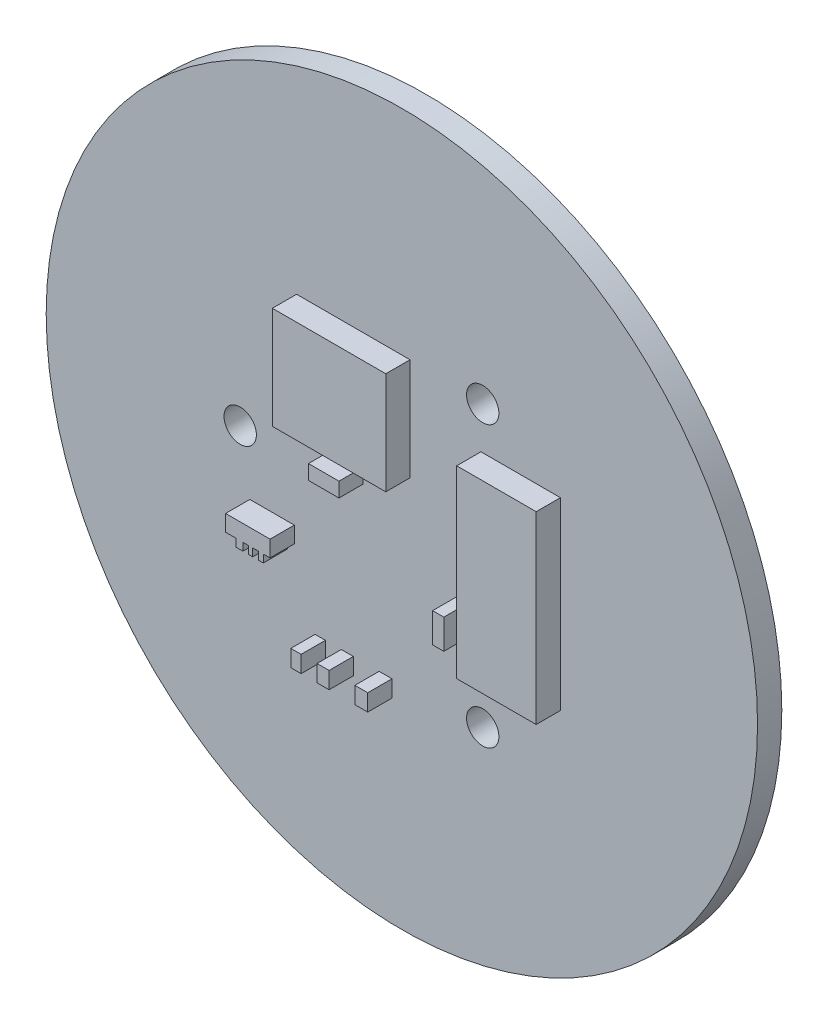
SolidWorks part; units mm, degrees
ref_plane "前视基准面" through (0, 0, 0) normal (0, 0, 1) x (1, 0, 0)
ref_plane "上视基准面" through (0, 0, 0) normal (0, 1, 0) x (1, 0, 0)
ref_plane "右视基准面" through (0, 0, 0) normal (1, 0, 0) x (0, 0, -1)
sketch "草图1" plane through (0, 0, 0) normal (0, 0, 1) x (1, 0, 0)
  circle A0 centre (0, 0) radius 22
extrude "凸台-拉伸1" add sketch "草图1" along normal blind 1.5
sketch "草图2" plane through (0, 0, 0) normal (0, 0, -1) x (-1, 0, 0)
  line L2 (2, 2.5) -> (2, -2.5)
  line L7 (-2, -2.5) -> (-2, 2.5)
  line L8 (2, -2.5) -> (-2, -2.5)
  line L9 (-2, 2.5) -> (2, 2.5)
extrude "凸台-拉伸2" add sketch "草图2" along normal blind 1.8
sketch "草图3" plane through (0, 0, 0) normal (0, 0, -1) x (-1, 0, 0)
  circle A1 centre (10, 0) radius 1
  circle A2 centre (-5, 8.6603) radius 1
  circle A3 centre (-5, -8.6603) radius 1
extrude "切除-拉伸1" cut sketch "草图3" against normal blind 1.8
sketch "草图4" plane through (0, 0, 1.5) normal (0, 0, 1) x (1, 0, 0)
  line L0 (-8.1056, -3.6542) -> (-6.6543, -3.6542)
  line L1 (-6.511, 8.7833) -> (0.5049, 8.7833)
  line L2 (-6.511, 8.7833) -> (-6.511, 2.4582)
  line L3 (-6.511, 2.4582) -> (0.5049, 2.4582)
  line L4 (0.5049, 8.7833) -> (0.5049, 2.4582)
  line L5 (4.8899, 6.046) -> (9.8064, 6.046)
  line L6 (4.8899, 6.046) -> (4.8899, -5.355)
  line L7 (4.8899, -5.355) -> (9.8064, -5.355)
  line L8 (9.8064, 6.046) -> (9.8064, -5.355)
  line L9 (-4.2787, 1.5813) -> (-2.3918, 1.5813)
  line L10 (-4.2787, 1.5813) -> (-4.2787, 0.6777)
  line L11 (-4.2787, 0.6777) -> (-2.3918, 0.6777)
  line L12 (-2.3918, 1.5813) -> (-2.3918, 0.6777)
  line L13 (-5.3683, -8.863) -> (-4.7305, -8.863)
  line L14 (-5.3683, -8.863) -> (-5.3683, -9.8994)
  line L15 (-5.3683, -9.8994) -> (-4.7305, -9.8994)
  line L16 (-4.7305, -8.863) -> (-4.7305, -9.8994)
  line L17 (-3.7472, -8.863) -> (-3.0031, -8.863)
  line L18 (-3.7472, -8.863) -> (-3.7472, -9.8994)
  line L19 (-3.7472, -9.8994) -> (-3.0031, -9.8994)
  line L20 (-3.0031, -8.863) -> (-3.0031, -9.8994)
  line L21 (-1.4085, -8.863) -> (-0.6112, -8.863)
  line L22 (-1.4085, -8.863) -> (-1.4085, -9.8994)
  line L23 (-1.4085, -9.8994) -> (-0.6112, -9.8994)
  line L24 (-0.6112, -8.863) -> (-0.6112, -9.8994)
  line L25 (3.4017, -2.4582) -> (4.0927, -2.4582)
  line L26 (3.4017, -2.4582) -> (3.4017, -4.292)
  line L27 (3.4017, -4.292) -> (4.0927, -4.292)
  line L28 (4.0927, -2.4582) -> (4.0927, -4.292)
  line L29 (-6.6543, -3.6542) -> (-6.6543, -4.6614)
  line L30 (-6.6543, -4.6614) -> (-7.0705, -4.6614)
  line L31 (-7.0705, -4.6614) -> (-7.0705, -5.1407)
  line L32 (-7.0705, -5.1407) -> (-7.3799, -5.1407)
  line L33 (-7.3799, -5.1407) -> (-7.3799, -4.6614)
  line L34 (-7.3799, -4.6614) -> (-7.7264, -4.6614)
  line L35 (-7.7264, -4.6614) -> (-7.7264, -5.1407)
  line L36 (-7.7264, -5.1407) -> (-7.9912, -5.1407)
  line L37 (-7.9912, -5.1407) -> (-7.9912, -4.6614)
  line L38 (-7.9912, -4.6614) -> (-8.3317, -4.6614)
  line L39 (-8.3317, -4.6614) -> (-8.3317, -5.1407)
  line L40 (-8.3317, -5.1407) -> (-8.748, -5.1407)
  line L41 (-8.748, -5.1407) -> (-8.748, -4.6614)
  line L42 (-8.748, -4.6614) -> (-9.4038, -4.6614)
  line L43 (-9.4038, -4.6614) -> (-9.4038, -3.6542)
  line L44 (-9.4038, -3.6542) -> (-8.1056, -3.6542)
extrude "凸台-拉伸3" add sketch "草图4" along normal blind 1.5
